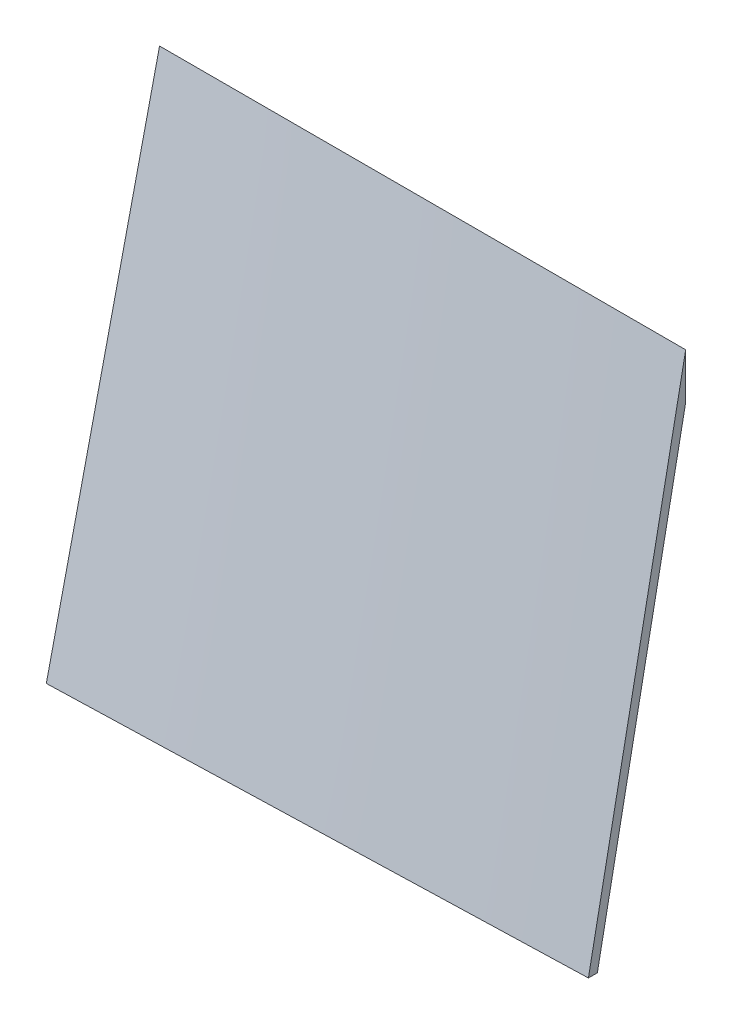
SolidWorks part; units mm, degrees
ref_plane "Vorderansicht-XY" through (0, 0, 0) normal (0, 0, 1) x (1, 0, 0)
ref_plane "Draufsicht-ZX" through (0, 0, 0) normal (0, 1, 0) x (1, 0, 0)
ref_plane "Seitenansicht-YZ" through (0, 0, 0) normal (1, 0, 0) x (0, 0, -1)
sketch "Skizze1" plane through (0, 0, 0) normal (1, 0, 0) x (0, 0, -1)
  line L0 (-118.8722, 0) -> (0, 520.1174)
  line L1 (55, 0) -> (-55, 0) construction
  line L2 (0, 55) -> (0, -55) construction
  line L3 (0, 520.1174) -> (0, 565)
  line L4 (0, 565) -> (-129.13, 0)
  line L5 (-129.13, 0) -> (-118.8722, 0)
  dimension "D1" = 10
  dimension "D2" = 129.13
  dimension "D3" = 565
ref_plane "Ebene1" through (600, 0, 0) normal (1, 0, 0) x (0, 0, -1)
sketch "Skizze2" plane through (600, 0, 0) normal (1, 0, 0) x (0, 0, -1)
  line L0 (-100.7291, 0) -> (0, 513.0901)
  line L1 (71.0215, 0) -> (-71.0215, 0) construction
  line L2 (0, 310.75) -> (0, -310.75) construction
  line L3 (0, 513.0901) -> (0, 565)
  line L4 (0, 565) -> (-110.92, 0)
  line L5 (-110.92, 0) -> (-100.7291, 0)
  dimension "D1" = 110.92
  dimension "D2" = 565
  dimension "D3" = 10
loft "Ausformung1" add profiles "Skizze1", "Skizze2"
